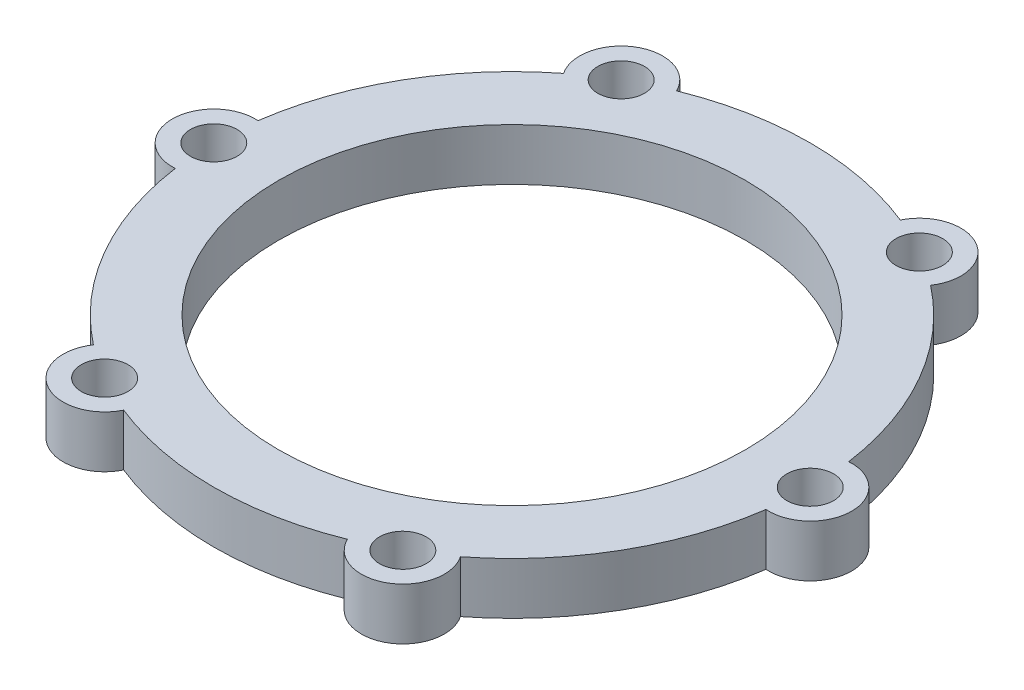
SolidWorks part; units mm, degrees
ref_plane "Front Plane" through (0, 0, 0) normal (0, 0, 1) x (1, 0, 0)
ref_plane "Top Plane" through (0, 0, 0) normal (0, 1, 0) x (1, 0, 0)
ref_plane "Right Plane" through (0, 0, 0) normal (1, 0, 0) x (0, 0, -1)
sketch "Sketch2" plane through (0, 0, 0) normal (0, 1, 0) x (1, 0, 0)
  line L0 (0, 0) -> (127.7494, 0) construction
  line L1 (0, 0) -> (54.7673, 94.8598) construction
  arc A0 (21.5603, 53.3048) -> (-21.5603, 53.3048) centre (0, 0) ccw
  circle A1 centre (0, 0) radius 45
  circle A2 centre (28.75, 49.7965) radius 8
  circle A3 centre (28.75, 49.7965) radius 4.5
  circle A4 centre (57.5, 0) radius 4.5
  circle A5 centre (57.5, 0) radius 8
  circle A6 centre (28.75, -49.7965) radius 4.5
  circle A7 centre (28.75, -49.7965) radius 8
  circle A8 centre (-28.75, -49.7965) radius 4.5
  circle A9 centre (-28.75, -49.7965) radius 8
  circle A10 centre (-57.5, 0) radius 4.5
  circle A11 centre (-57.5, 0) radius 8
  circle A12 centre (-28.75, 49.7965) radius 4.5
  circle A13 centre (-28.75, 49.7965) radius 8
  arc A14 (-35.3832, 45.3242) -> (-56.9435, 7.9806) centre (0, 0) ccw
  arc A15 (-56.9435, -7.9806) -> (-35.3832, -45.3242) centre (0, 0) ccw
  arc A16 (-21.5603, -53.3048) -> (21.5603, -53.3048) centre (0, 0) ccw
  arc A17 (35.3832, -45.3242) -> (56.9435, -7.9806) centre (0, 0) ccw
  arc A18 (56.9435, 7.9806) -> (35.3832, 45.3242) centre (0, 0) ccw
  arc A19 (57.3239, -4.4966) -> (57.3239, 4.4966) centre (0, 0) ccw
  point P1 (0, 0)
  point P28 (0, 0)
  dimension "D1" = 115
  dimension "D2" = 90
  dimension "D4" = 16
  dimension "D5" = 9
  dimension "D3" = 60
  dimension "D6" = 6
extrude "Boss-Extrude1" add sketch "Sketch2" along normal blind 10 contours A5 A18 A2 A0 A13 A14 A11 A15 A9 A16 A7 A17 A1 | A13 A12 | A11 A10 | A9 A8 | A7 A6 | A5 A4 | A2 A3
